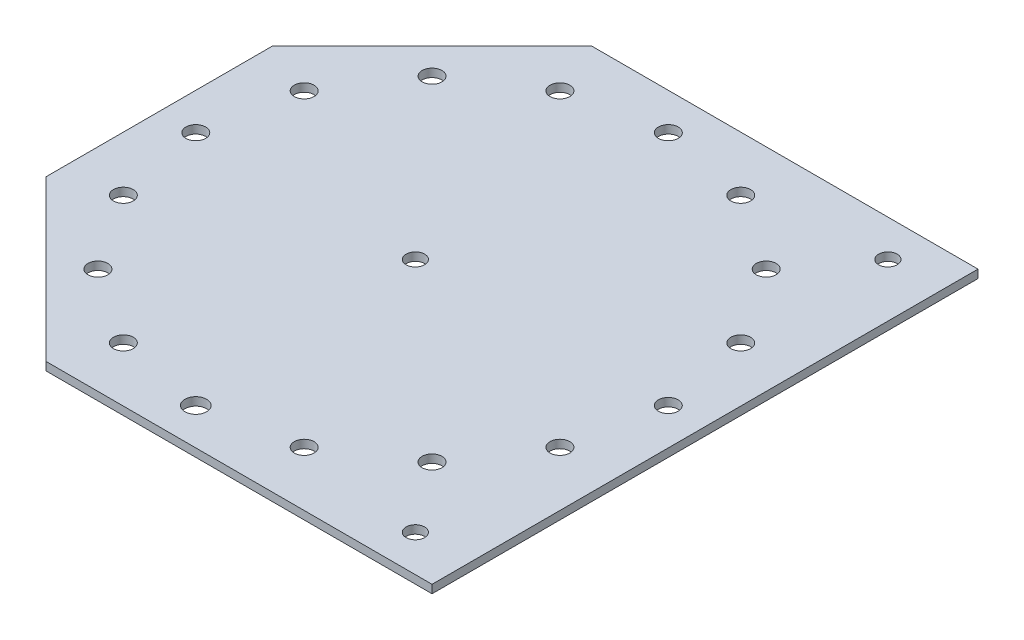
SolidWorks part; units mm, degrees
ref_plane "Front Plane" through (0, 0, 0) normal (0, 0, 1) x (1, 0, 0)
ref_plane "Top Plane" through (0, 0, 0) normal (0, 1, 0) x (1, 0, 0)
ref_plane "Right Plane" through (0, 0, 0) normal (1, 0, 0) x (0, 0, -1)
sketch "Sketch1" plane through (0, 0, 0) normal (0, 1, 0) x (1, 0, 0)
  line L0 (-88.6314, 0) -> (162.72, 0) construction
  line L1 (0, 60.875) -> (0, -60.875) construction
  line L2 (-79.7898, -60.875) -> (81.4786, -60.875) construction
  line L3 (-60.875, 60.875) -> (-60.875, -60.875) construction
  line L4 (-88.6314, 60.875) -> (81.4786, 60.875) construction
  line L5 (60.875, 60.875) -> (60.875, -60.875) construction
  line L6 (-86.0903, 0) -> (0, -86.0903) construction
  line L7 (0, -86.0903) -> (86.0903, 0) construction
  line L8 (86.0903, 0) -> (0, 86.0903) construction
  line L9 (0, 86.0903) -> (-86.0903, 0) construction
  line L10 (-99.4653, 60.875) -> (-99.4653, -41.1995) construction
  line L11 (-19.4653, 60.875) -> (-19.4653, -60.875) construction
  line L12 (0, 0) -> (-60.875, -60.875) construction
  line L13 (80.0047, 60.875) -> (80.0047, -60.875) construction
  line L14 (-88.6314, 0) -> (81.4786, 0) construction
  line L15 (0, 0) -> (-79.537, -32.9453) construction
  line L16 (86.0903, 0) -> (-45.4651, 131.5554) construction
  line L17 (-41.1995, 99.4652) -> (99.4653, 99.4652)
  line L18 (-99.4652, 41.1995) -> (-99.4652, -41.1995)
  line L19 (99.4653, 0) -> (99.4653, 165.2125) construction
  line L20 (-41.1995, 99.4652) -> (-99.4653, 41.1995)
  line L21 (0, 0) -> (-99.4652, 99.4652) construction
  line L22 (-41.1995, -99.4652) -> (99.4653, -99.4652)
  line L23 (99.4653, -99.4652) -> (99.4653, 99.4652)
  line L24 (-27.2873, 113.3775) -> (-113.3775, 27.2873) construction
  line L25 (-41.1995, -99.4652) -> (-99.4652, -41.1995)
  line L26 (-88.6314, -60.875) -> (81.4786, -60.875) construction
  line L27 (-99.4653, 60.875) -> (-99.4653, -60.875) construction
  circle A0 centre (-60.875, -60.875) radius 3.375
  circle A1 centre (60.875, -60.875) radius 3.375
  circle A2 centre (0, 0) radius 86.0903 construction
  circle A3 centre (0, 0) radius 99.4653 construction
  arc A5 (99.4653, 83.8619) -> (99.4653, -83.8619) centre (80.0047, 0) ccw construction
  arc A6 (39.9965, 91.0693) -> (99.4653, -97.5478) centre (80.0047, 0) ccw construction
  circle A8 centre (0, -86.0903) radius 3.9511
  circle A9 centre (-86.0903, 0) radius 3.6069
  circle A10 centre (-79.537, 32.9453) radius 3.6069
  circle A11 centre (-60.875, 60.875) radius 3.6069
  circle A12 centre (-32.9453, 79.537) radius 3.6069
  circle A13 centre (0, 86.0903) radius 3.6069
  circle A14 centre (32.9453, 79.537) radius 3.6069
  circle A15 centre (60.875, 60.875) radius 3.6069
  circle A16 centre (79.537, 32.9453) radius 3.6069
  circle A17 centre (86.0903, 0) radius 3.6069
  circle A18 centre (79.537, -32.9453) radius 3.6069
  circle A19 centre (60.875, -60.875) radius 3.6069
  circle A20 centre (32.9453, -79.537) radius 3.6069
  circle A21 centre (0, -86.0903) radius 3.6069
  circle A22 centre (-32.9453, -79.537) radius 3.6069
  circle A23 centre (-60.875, -60.875) radius 3.6069
  circle A24 centre (-79.537, -32.9453) radius 3.6069
  circle A25 centre (80.0048, -86.0902) radius 3.375
  circle A27 centre (-6.0855, 0) radius 3.375
  circle A29 centre (80.0048, 86.0903) radius 3.375
  point P74 (0, 0)
  point P87 (80.0048, 0)
  dimension "D5" = 6.75
  dimension "D6" = 6.75
  dimension "D7" = 121.75
  dimension "D13" = 198.9305
  dimension "D11" = 172.1805
  dimension "D19" = 38.59
  dimension "D10" = 121.75
  dimension "D12" = 80
  dimension "D14" = 99.4653
  dimension "D16" = 99.47
  dimension "D9" = 80.0047
  dimension "D17" = 22.5
  dimension "D1" = 60.875
  dimension "D2" = 60.875
  dimension "D3" = 60.875
  dimension "D4" = 60.875
  dimension "D8" = 13.375
  dimension "D15" = 99.47
  dimension "D18" = 16
extrude "Boss-Extrude1" add sketch "Sketch1" along normal blind 3 contours L25 L22 L23 L17 L20 L18 A29 A27 A25 A24 A23 A22 A20 A19 A18 A17 A16 A15 A14 A13 A12 A11 A10 A9 A8
